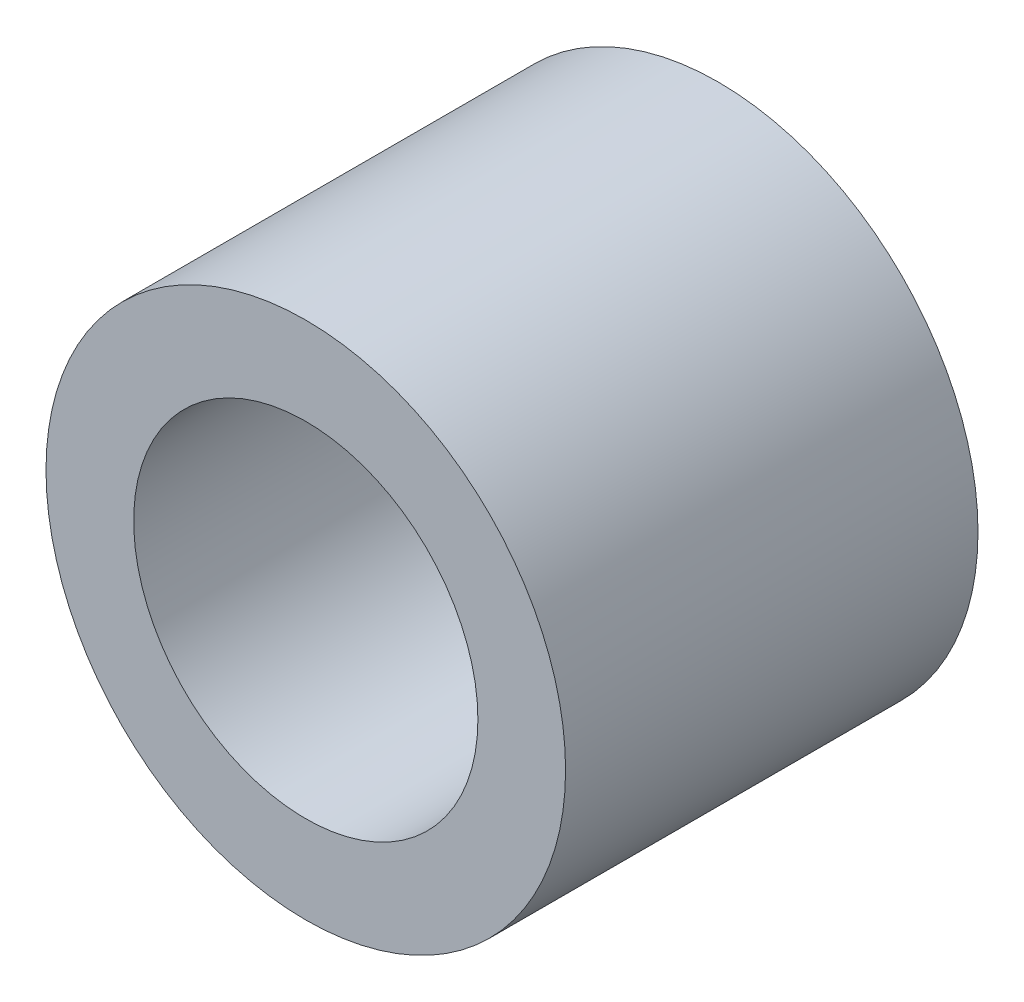
SolidWorks part; units mm, degrees
material "3003-H12, Barre (SS)"
ref_plane "Plane1" through (0, 0, 0) normal (0, 0, 1) x (1, 0, 0)
ref_plane "Plane2" through (0, 0, 0) normal (0, 1, 0) x (1, 0, 0)
ref_plane "Plane3" through (0, 0, 0) normal (1, 0, 0) x (0, 0, -1)
sketch "Sketch1" plane through (0, 0, 0) normal (0, 0, 1) x (1, 0, 0)
  circle A0 centre (0, 0) radius 2.65
  circle A1 centre (0, 0) radius 4
  dimension "D1" = 8
  dimension "D2" = 5.3
extrude "Extrude1" add sketch "Sketch1" along normal mid plane 6.35
